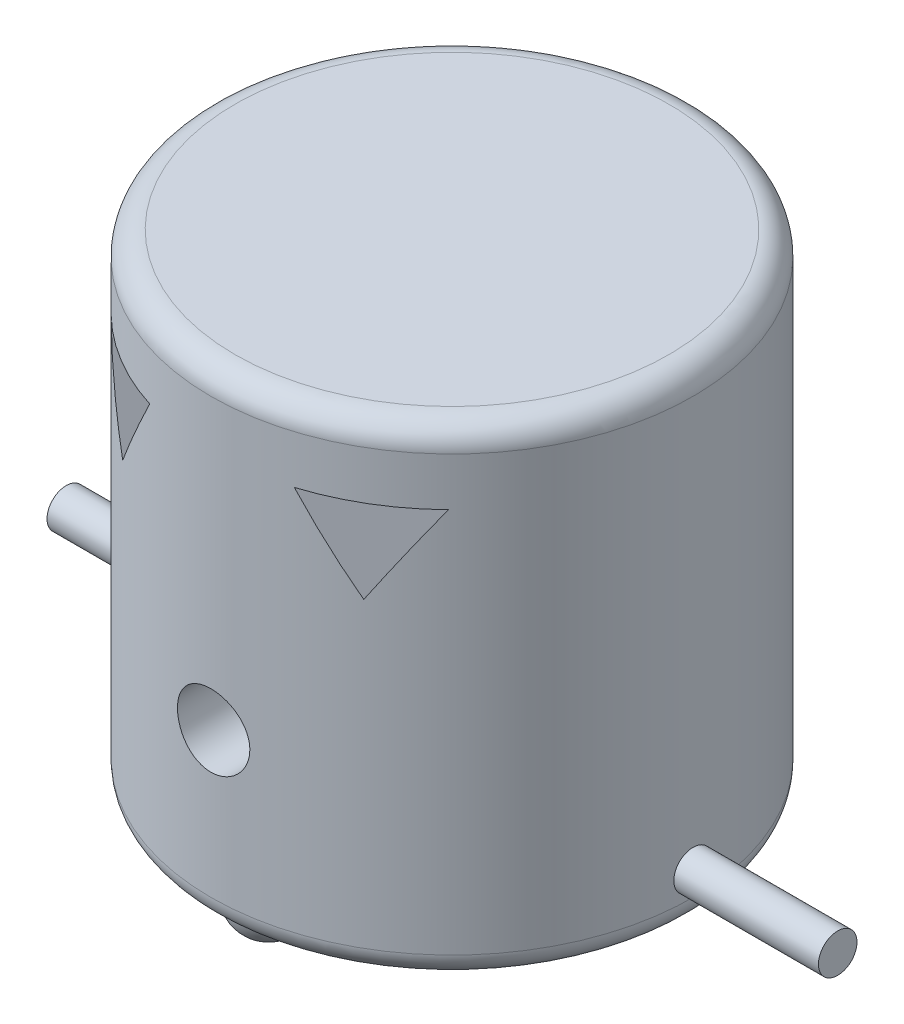
SolidWorks part; units mm, degrees
ref_plane "Plan de face" through (0, 0, 0) normal (0, 0, 1) x (1, 0, 0)
ref_plane "Plan de dessus" through (0, 0, 0) normal (0, 1, 0) x (1, 0, 0)
ref_plane "Plan de droite" through (0, 0, 0) normal (1, 0, 0) x (0, 0, -1)
sketch "Esquisse1" plane through (0, 0, 0) normal (0, 1, 0) x (1, 0, 0)
  circle A0 centre (0, 0) radius 50
  dimension "D1" = 100
extrude "Boss.-Extru.1" add sketch "Esquisse1" along normal blind 100
ref_plane "Plan1" through (50, 0, 0) normal (1, 0, 0) x (0, 0, -1)
ref_plane "Plan2" through (-50, 0, 0) normal (-1, 0, 0) x (0, 0, 1)
sketch "Esquisse2" plane through (50, 0, 0) normal (1, 0, 0) x (0, 0, -1)
  circle A0 centre (0, 10) radius 4
  point P2 (0, 0)
  dimension "D1" = 8
  dimension "D2" = 10
extrude "Boss.-Extru.2" add sketch "Esquisse2" along normal blind 30 separate body
sketch "Esquisse3" plane through (-50, 0, 0) normal (-1, 0, 0) x (0, 0, 1)
  line L0 (-50, 0) -> (50, 0) construction
  circle A0 centre (0, 10) radius 4
  point P4 (0, 0)
  dimension "D1" = 8
  dimension "D2" = 10
extrude "Boss.-Extru.3" add sketch "Esquisse3" along normal blind 30 separate body
fillet "Congé1" radius 5 2 edges at (0, 0, 50) (0, 100, 50)
sketch "Esquisse5" plane through (0, 0, 0) normal (1, 0, 0) x (0, 0, -1)
  line L0 (-38, 0) -> (-38, -7.4)
  line L3 (0, 39.4555) -> (0, -22.9359) construction
  line L7 (-30.6, 0) -> (-38, 0)
  arc A0 (-38, -7.4) -> (-30.6, 0) centre (-38, 0) ccw
  point P3 (-37.4065, -1.7396)
  point P8 (0, 0)
  point P9 (-45, 0.3972)
  dimension "D1" = 7.4
  dimension "D2" = 38
revolve "Révolution1" add sketch "Esquisse5" angle 360 about L0
mirror "Symétrie4" about plane through (0, 0, 0) normal (0, 0, 1) of "Révolution1"
sketch "Esquisse6" plane through (0, 0, 0) normal (0, 0, 1) x (1, 0, 0)
  line L0 (0, 108.0899) -> (0, -2.4901) construction
  line L1 (-35, 85) -> (-15, 85)
  line L2 (-15, 85) -> (-25, 67.6795)
  line L3 (-25, 67.6795) -> (-35, 85)
  line L5 (45, 100) -> (-45, 100) construction
  line L6 (-45, 0) -> (-2.6106, 0) construction
  line L7 (25, 67.6795) -> (35, 85)
  line L8 (15, 85) -> (25, 67.6795)
  line L9 (35, 85) -> (15, 85)
  circle A0 centre (0, 35) radius 7.5
  point P5 (0, 46.8759)
  point P7 (-25, 85)
  point P10 (0, 0)
  point P13 (0, 0)
  point P14 (0, 48.3569)
  point P15 (0, 36.5091)
  point P16 (0, 108.0899)
  point P17 (0, 38.9774)
  point P18 (0, 33.0534)
  dimension "D5" = 15
  dimension "D1" = 20
  dimension "D2" = 20
  dimension "D3" = 25
  dimension "D4" = 15
  dimension "D6" = 35
extrude "Enlèv. mat.-Extru.1" cut sketch "Esquisse6" along normal blind 65
